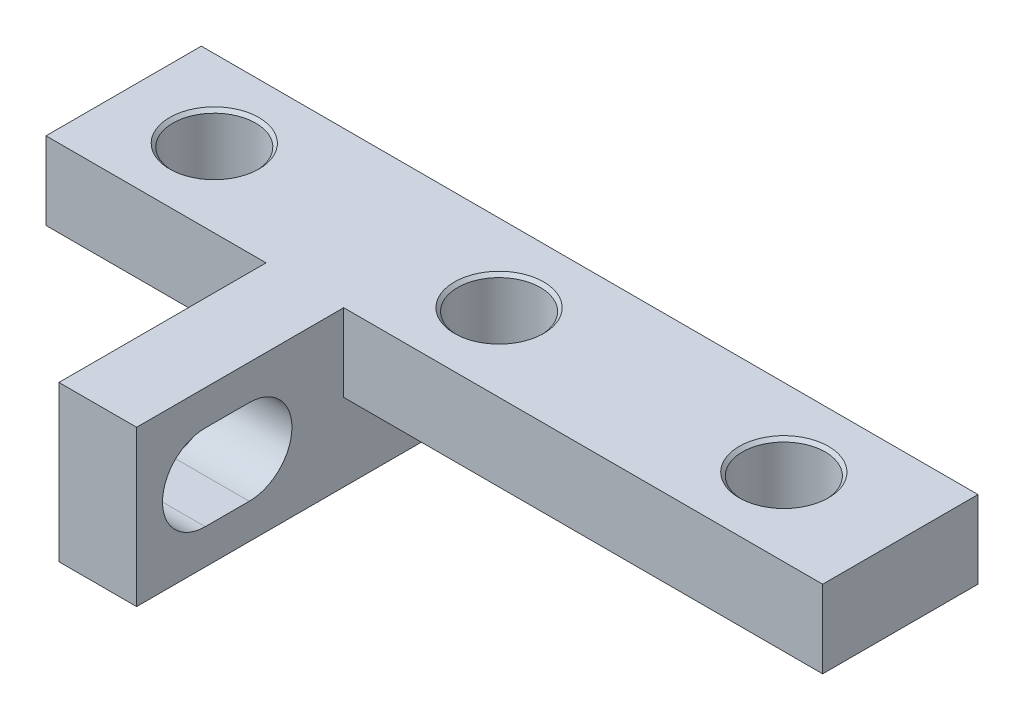
SolidWorks part; units mm, degrees
ref_plane "Front" through (0, 0, 0) normal (0, 0, 1) x (1, 0, 0)
ref_plane "Top" through (0, 0, 0) normal (0, 1, 0) x (1, 0, 0)
ref_plane "Right" through (0, 0, 0) normal (1, 0, 0) x (0, 0, -1)
sketch "Эскиз1" plane through (0, 0, 0) normal (0, 0, 1) x (1, 0, 0)
  line L0 (-1.5, 0) -> (-1.5, 22)
  line L1 (-1.5, 22) -> (-20, 22)
  line L2 (-20, 22) -> (-20, 25)
  line L3 (-20, 25) -> (20, 25)
  line L4 (20, 25) -> (20, 22)
  line L5 (20, 22) -> (1.5, 22)
  line L6 (1.5, 22) -> (1.5, 0)
  line L7 (1.5, 0) -> (-1.5, 0)
  line L8 (0, 0) -> (0, 25) construction
  dimension "D1" = 3
  dimension "D2" = 3
  dimension "D3" = 40
  dimension "D4" = 25
extrude "Бобышка-Вытянуть1" add sketch "Эскиз1" along normal blind 14
sketch "Эскиз2" plane through (0, 0, 14) normal (0, 0, 1) x (1, 0, 0)
  line L0 (20, 25) -> (-20, 25) construction
  line L1 (-10, 19) -> (20, 19)
  line L2 (-10, 19) -> (-10, 25)
  line L3 (-10, 25) -> (20, 25)
  line L4 (20, 19) -> (20, 25)
  line L5 (-10, 19) -> (20, 25) construction
  line L6 (-10, 25) -> (20, 19) construction
  line L7 (20, 22) -> (20, 25) construction
  point P0 (5, 22)
  line M1 (-1.5, 0) -> (1.5, 0)
  line M2 (1.5, 0) -> (1.5, 22)
  line M5 (20, 25) -> (-20, 25)
  line M6 (-20, 25) -> (-20, 22)
  line M7 (-20, 22) -> (-1.5, 22)
  line M8 (-1.5, 22) -> (-1.5, 0)
  dimension "D1" = 30
  dimension "D2" = 6
extrude "Вырез-Вытянуть1" cut sketch "Эскиз2" against normal through all contours L2 M7 M5 M6 | L1 M8 M1 M2
sketch "Эскиз3" plane through (0, 0, 14) normal (0, 0, 1) x (1, 0, 0)
  line L0 (-1.5, 22) -> (-1.5, 25)
  line L1 (20, 25) -> (-10, 25) construction
  line L2 (1.5, 22) -> (1.5, 25)
extrude "Вырез-Вытянуть3" cut sketch "Эскиз3" against normal offset from surface (8 mm away) 6 up to face at (2.5, 22, 0)
hole_wizard "Отверстие с зазором M31" positions "Эскиз5" profile "Эскиз4" hole size "M3" standard "DIN" end condition through all
sketch "Эскиз5" plane through (0, 22, 0) normal (0, -1, 0) x (1, 0, 0)
  line L1 (1.5, 0) -> (20, 0) construction
  line L2 (-10, 0) -> (-10, 6) construction
  point P0 (-6.5, 3)
  point P1 (15.5, 3)
  point P11 (4.5, 3)
  dimension "D1" = 22
  dimension "D2" = 3
  dimension "D3" = 3.5
  dimension "D4" = 11
sketch "Эскиз4" plane through (-6.5, 22, 3) normal (1, 0, 0) x (0, 0, -1)
  line L0 (0, 0) -> (0, 3)
  line L1 (0, 3) -> (1.725, 3)
  line L2 (1.6, 2.875) -> (1.6, 0.125)
  line L3 (1.6, 0.125) -> (1.725, 0)
  line L5 (1.725, 0) -> (0, 0)
  line L6 (-1.6, 0.125) -> (-1.725, 0) construction
  line L7 (1.725, 3) -> (1.6, 2.875)
  line L8 (-1.725, 3) -> (-1.6, 2.875) construction
  line L11 (0, -6.35) -> (0, 107.95) construction
  dimension "Диаметр сквозного отверстия" = 3.2
  dimension "Глубина сквозного отверстия" = 3
  dimension "Диаметр передней зенковки" = 3.45
  dimension "Угол передней зенковки" = 90
  dimension "Диаметр задней зенковки" = 3.45
  dimension "Угол задней зенковки" = 90
sketch "Эскиз6" plane through (1.5, 0, 0) normal (1, 0, 0) x (0, 0, -1)
  line L0 (-11.35, 22) -> (-9.65, 22) construction
  line L1 (-11.35, 23.65) -> (-9.65, 23.65)
  line L2 (-11.35, 20.35) -> (-9.65, 20.35)
  line L3 (-6, 25) -> (0, 25) construction
  line L4 (-13, 22) -> (-13, 19) construction
  line L5 (0, 19) -> (-14, 19) construction
  line L9 (-14, 19) -> (-14, 25) construction
  arc A0 (-11.35, 23.65) -> (-11.35, 20.35) centre (-11.35, 22) ccw
  arc A1 (-9.65, 20.35) -> (-9.65, 23.65) centre (-9.65, 22) ccw
  point P2 (-10.5, 22)
  dimension "D1" = 3.3
  dimension "D2" = 5
  dimension "D3" = 3
  dimension "D4" = 1
extrude "Вырез-Вытянуть4" cut sketch "Эскиз6" against normal up to next
